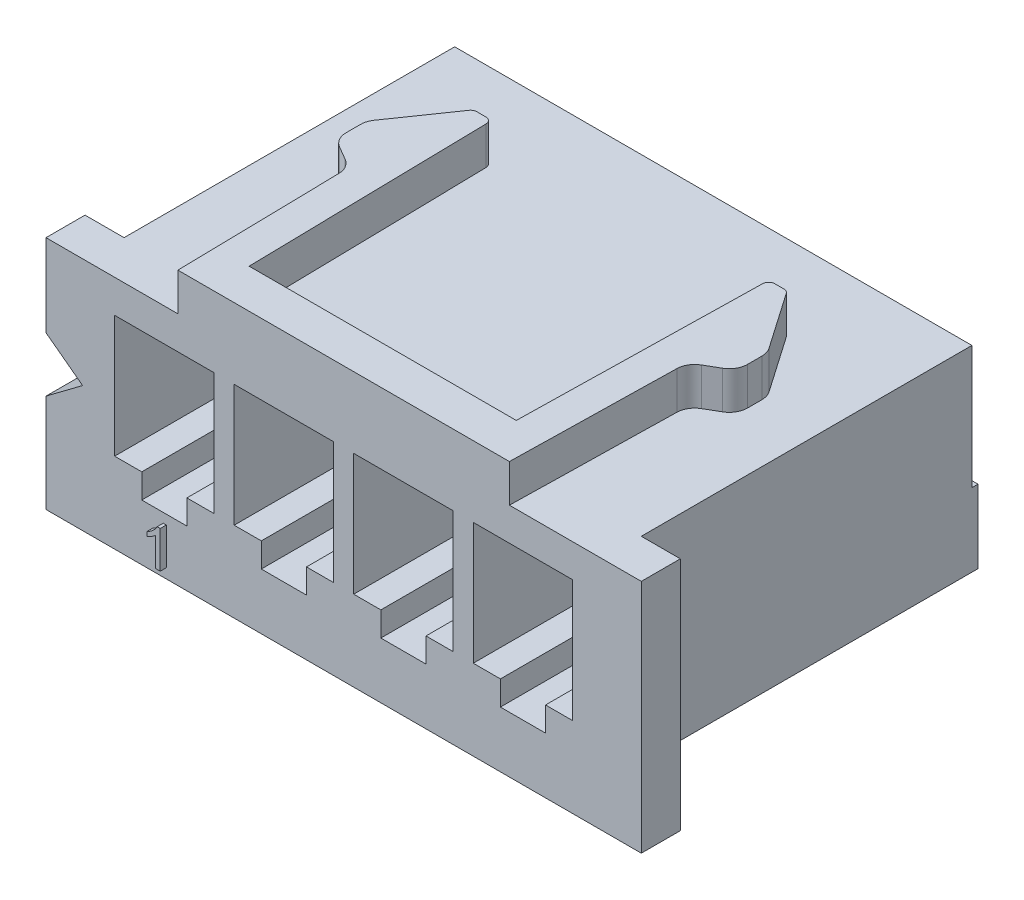
SolidWorks part; units mm, degrees
ref_plane "Front" through (0, 0, 0) normal (0, 0, 1) x (1, 0, 0)
ref_plane "Top" through (0, 0, 0) normal (0, 1, 0) x (1, 0, 0)
ref_plane "Right" through (0, 0, 0) normal (1, 0, 0) x (0, 0, -1)
sketch "Sketch1" plane through (0, 0, 0) normal (0, 0, 1) x (1, 0, 0)
  line L0 (-5.3848, -2.0447) -> (5.3848, 2.0447) construction
  line L1 (-5.3848, 2.0447) -> (5.3848, 2.0447)
  line L2 (-5.3848, 2.0447) -> (-5.3848, -2.0447)
  line L3 (-5.3848, -2.0447) -> (5.3848, -2.0447)
  line L4 (5.3848, 2.0447) -> (5.3848, -2.0447)
  dimension "D1" = 10.7696
  dimension "D2" = 4.0894
extrude "BODY" add sketch "Sketch1" against normal blind 7.6962
sketch "Sketch2" plane through (0, 0, 0) normal (0, 0, 1) x (1, 0, 0)
  line L0 (5.3848, -2.0447) -> (5.3848, 2.0447) construction
  line L1 (-5.3848, -2.0447) -> (5.3848, -2.0447) construction
  line L2 (-5.3848, 2.0447) -> (-5.3848, -2.0447) construction
  line L3 (5.3848, -2.0447) -> (5.3848, 2.0447)
  line L4 (-5.3848, -2.0447) -> (5.3848, -2.0447)
  line L5 (-5.3848, 2.0447) -> (-5.3848, -2.0447)
  line L6 (-6.1976, 2.0447) -> (-6.1976, -2.8575)
  line L7 (-6.1976, -2.8575) -> (6.1976, -2.8575)
  line L8 (6.1976, -2.8575) -> (6.1976, 2.0447)
  line L9 (-6.1976, 2.0447) -> (-5.3848, 2.0447)
  line L10 (5.3848, 2.0447) -> (6.1976, 2.0447)
  dimension "D1" = 0.8128
extrude "FLANGE" add sketch "Sketch2" against normal blind 0.8128
sketch "Sketch3" plane through (0, 2.0447, 0) normal (0, 1, 0) x (-1, 0, 0)
  line L0 (-3.4512, 0) -> (-3.5186, -3.418)
  line L1 (-6.1976, 0) -> (6.1976, 0) construction
  line L2 (-3.708, -3.7399) -> (-3.9888, -3.903)
  line L3 (-4.1783, -4.2324) -> (-4.1783, -4.5292)
  line L4 (-4.1106, -4.7461) -> (-3.3018, -5.9143)
  line L5 (-3.1974, -5.969) -> (-3.0074, -5.969)
  line L6 (-2.8804, -5.8445) -> (-2.7813, -0.8128)
  line L7 (-2.7813, -0.8128) -> (2.7813, -0.8128)
  line L8 (0, 0) -> (0, -7.6962) construction
  line L9 (3.4512, 0) -> (-3.4512, 0)
  line L10 (-5.3848, -7.6962) -> (-5.3848, -0.8128) construction
  line L11 (-5.3848, -7.6962) -> (5.3848, -7.6962) construction
  line L12 (2.8804, -5.8445) -> (2.7813, -0.8128)
  line L13 (3.1974, -5.969) -> (3.0074, -5.969)
  line L14 (4.1106, -4.7461) -> (3.3018, -5.9143)
  line L15 (4.1783, -4.2324) -> (4.1783, -4.5292)
  line L16 (3.708, -3.7399) -> (3.9888, -3.903)
  line L17 (3.4512, 0) -> (3.5186, -3.418)
  arc A0 (-3.3018, -5.9143) -> (-3.1974, -5.969) centre (-3.1974, -5.842) ccw
  arc A1 (-2.8804, -5.8445) -> (-3.0074, -5.969) centre (-3.0074, -5.842) cw
  arc A2 (-4.1783, -4.5292) -> (-4.1106, -4.7461) centre (-3.7973, -4.5292) ccw
  arc A3 (-3.9888, -3.903) -> (-4.1783, -4.2324) centre (-3.7973, -4.2324) ccw
  arc A4 (-3.5186, -3.418) -> (-3.708, -3.7399) centre (-3.8995, -3.4105) cw
  arc A5 (3.5186, -3.418) -> (3.708, -3.7399) centre (3.8995, -3.4105) ccw
  arc A6 (3.9888, -3.903) -> (4.1783, -4.2324) centre (3.7973, -4.2324) cw
  arc A7 (4.1783, -4.5292) -> (4.1106, -4.7461) centre (3.7973, -4.5292) cw
  arc A8 (2.8804, -5.8445) -> (3.0074, -5.969) centre (3.0074, -5.842) ccw
  arc A9 (3.3018, -5.9143) -> (3.1974, -5.969) centre (3.1974, -5.842) cw
  point P10 (3.5228, -3.6322)
  point P16 (-3.2639, -5.969)
  point P19 (-2.8829, -5.969)
  point P22 (-4.1783, -4.6482)
  point P25 (-4.1783, -4.0132)
  point P28 (-3.5228, -3.6322)
  point P49 (0, -0.8128)
  point P50 (4.1783, -4.0132)
  point P51 (4.1783, -4.6482)
  point P52 (2.8829, -5.969)
  point P53 (3.2639, -5.969)
  dimension "D11" = 0.127
  dimension "D12" = 0.381
  dimension "D1" = 0.8128
  dimension "D2" = 1.2065
  dimension "D3" = 5.969
  dimension "D4" = 2.3368
  dimension "D5" = 0.635
  dimension "D6" = 1.2954
  dimension "D7" = 1.397
  dimension "D8" = 0.6858
  dimension "D9" = 1.3208
  dimension "D10" = 0.381
extrude "LOCK" add sketch "Sketch3" along normal blind 0.7874
sketch "Sketch4" plane through (0, 0, 0) normal (0, 0, 1) x (1, 0, 0)
  line L0 (-3.7338, 1.3589) -> (-3.7338, -1.1811) construction
  line L1 (-4.7689, 1.3589) -> (-2.6988, 1.3589)
  line L2 (-4.7689, 1.3589) -> (-4.7689, -1.1811)
  line L3 (-4.7689, -1.1811) -> (-2.6987, -1.1811)
  line L4 (-2.6988, 1.3589) -> (-2.6987, -1.1811)
  line L5 (-2.6987, 0.0889) -> (-4.7689, 0.0889) construction
  line L6 (-5.3848, 2.0447) -> (-5.3848, -2.0447) construction
  line L7 (-3.4512, 2.0447) -> (-6.1976, 2.0447) construction
  dimension "D1" = 2.54
  dimension "D2" = 2.0701
  dimension "D3" = 1.651
  dimension "D4" = 0.6858
extrude "PIN CAVITY" cut sketch "Sketch4" against normal blind 7.0612
sketch "Sketch5" plane through (0, 0, -7.0612) normal (0, 0, 1) x (1, 0, 0)
  line L0 (-3.7338, 1.3589) -> (-3.7338, -1.1811) construction
  line L1 (-4.1339, 0.8954) -> (-3.3338, 0.8954)
  line L2 (-4.1339, 0.8954) -> (-4.1339, 0.0953)
  line L3 (-4.1339, 0.0953) -> (-3.3338, 0.0953)
  line L4 (-3.3338, 0.8954) -> (-3.3338, 0.0953)
  line L5 (-2.6988, 1.3589) -> (-4.7689, 1.3589) construction
  line L6 (-4.7689, -1.1811) -> (-2.6987, -1.1811) construction
  line L7 (-4.1339, 0.4953) -> (-3.3338, 0.4953) construction
  line L9 (5.3848, 2.0447) -> (-5.3848, 2.0447) construction
  dimension "D1" = 0.8001
  dimension "D2" = 1.5494
extrude "PIN ENTRY" cut sketch "Sketch5" against normal up to next (0.635 mm away)
sketch "Sketch6" plane through (0, 0, 0) normal (0, 0, 1) x (1, 0, 0)
  line L1 (-4.2037, -1.1811) -> (-3.2639, -1.1811)
  line L2 (-4.2037, -1.1811) -> (-4.2037, -1.6891)
  line L3 (-4.2037, -1.6891) -> (-3.2639, -1.6891)
  line L4 (-3.2639, -1.1811) -> (-3.2639, -1.6891)
  line L5 (-3.7338, 1.3589) -> (-3.7338, -2.8575) construction
  line L6 (-2.6988, 1.3589) -> (-4.7689, 1.3589) construction
  line L7 (-6.1976, -2.8575) -> (6.1976, -2.8575) construction
  line L10 (-4.7689, -1.1811) -> (-2.6987, -1.1811) construction
  line L11 (-4.7689, -1.1811) -> (-2.6987, -1.1811) construction
  dimension "D1" = 0.508
  dimension "D2" = 0.9398
extrude "PIN LOCK" cut sketch "Sketch6" against normal blind 3.175
sketch "Sketch8" plane through (0, 0, -7.6962) normal (0, 0, -1) x (-1, 0, 0)
  line L0 (-5.3848, -2.0447) -> (-5.3848, 2.0447) construction
  line L1 (-5.3848, -0.5207) -> (5.3848, -0.5207)
  line L2 (-5.3848, -0.5207) -> (-5.3848, -2.0447)
  line L3 (-5.3848, -2.0447) -> (5.3848, -2.0447)
  line L4 (5.3848, -0.5207) -> (5.3848, -2.0447)
  dimension "D1" = 1.524
extrude "BODY EXTEND" add sketch "Sketch8" along normal blind 0.127
sketch "Sketch7" plane through (0, -2.0447, 0) normal (0, -1, 0) x (1, 0, 0)
  line L1 (-4.3053, -7.8232) -> (-3.1623, -7.8232)
  line L2 (-4.3053, -7.8232) -> (-4.3053, -4.7752)
  line L3 (-4.3053, -4.7752) -> (-3.1623, -4.7752)
  line L4 (-3.1623, -7.8232) -> (-3.1623, -4.7752)
  line L5 (-3.7338, -4.7752) -> (-3.7338, -7.6962) construction
  line L7 (-3.3338, -7.6962) -> (-4.1339, -7.6962) construction
  line L9 (5.3848, -7.8232) -> (-5.3848, -7.8232) construction
  dimension "D1" = 1.143
  dimension "D2" = 3.048
extrude "PIN CAV CUTOUT" cut sketch "Sketch7" against normal blind 0.889
chamfer "Chamfer1" distance 0.127 angle 45 4 edges at (-4.1339, 0.4953, -7.6962) (-3.7338, 0.0953, -7.6962) (-3.3338, 0.4953, -7.6962) (-3.7338, 0.8954, -7.6962)
pattern_linear "4 POSITION" count 4 spacing 2.4892 along (1, 0, 0) of "Chamfer1", "PIN CAV CUTOUT", "PIN ENTRY", "PIN CAVITY", "PIN LOCK"
sketch "Sketch9" plane through (0, 0, 0) normal (0, 0, 1) x (1, 0, 0)
  line L0 (-6.1976, 0.3302) -> (-5.4356, -0.2413)
  line L1 (-6.1976, 2.0447) -> (-6.1976, -2.8575) construction
  line L2 (-5.4356, -0.2413) -> (-6.1976, -0.8128)
  line L3 (-6.1976, -0.8128) -> (-6.1976, 0.3302)
  line L4 (-5.4356, -0.2413) -> (-6.1976, -0.2413) construction
  line L5 (-3.4512, 2.0447) -> (-6.1976, 2.0447) construction
  dimension "D1" = 1.143
  dimension "D2" = 0.762
  dimension "D3" = 2.286
extrude "PIN 1 INDICATOR" cut sketch "Sketch9" against normal up to next
sketch "Sketch10" plane through (0, 0, 0) normal (0, 0, 1) x (1, 0, 0)
  line L0 (-3.7338, -1.6891) -> (-3.7338, -2.8575) construction
  line L1 (-4.2037, -1.6891) -> (-3.2639, -1.6891) construction
  line L2 (-6.1976, -2.8575) -> (6.1976, -2.8575) construction
  text T0 "1" font "Arial" height in points 3
  dimension "D1" = 0.3539
  dimension "D2" = 0.2032
extrude "PIN NUMBER" add sketch "Sketch10" along normal blind 0.127
